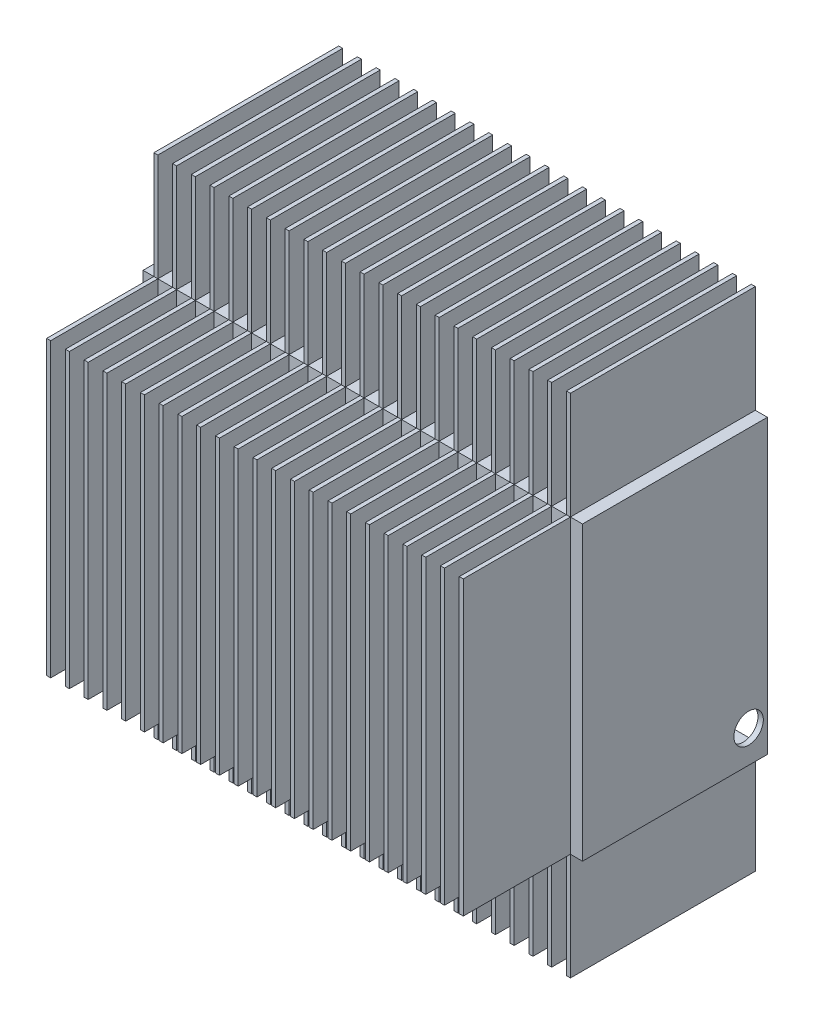
SolidWorks part; units mm, degrees
ref_plane "Front Plane" through (0, 0, 0) normal (0, 0, 1) x (1, 0, 0)
ref_plane "Top Plane" through (0, 0, 0) normal (0, 1, 0) x (1, 0, 0)
ref_plane "Right Plane" through (0, 0, 0) normal (1, 0, 0) x (0, 0, -1)
sketch "Sketch1" plane through (0, 0, 0) normal (0, 0, 1) x (1, 0, 0)
  line L1 (0, 0) -> (-164, 0)
  line L2 (0, 0) -> (0, 109)
  line L3 (0, 109) -> (-164, 109)
  line L4 (-164, 0) -> (-164, 109)
  dimension "D1" = 164
  dimension "D2" = 109
extrude "Boss-Extrude1" add sketch "Sketch1" against normal blind 69
sketch "Sketch2" plane through (0, 0, 0) normal (0, 0, 1) x (1, 0, 0)
  line L0 (0, 109) -> (-164, 109) construction
  line L1 (-160, 109) -> (-158.5, 109)
  line L2 (-160, 109) -> (-160, 0)
  line L3 (-160, 0) -> (-158.5, 0)
  line L4 (-158.5, 109) -> (-158.5, 0)
  line L5 (-164, 0) -> (0, 0) construction
  dimension "D1" = 4
  dimension "D2" = 1.5
extrude "Boss-Extrude3" add sketch "Sketch2" along normal blind 40 contours L2 L3 L4 L1
pattern_linear "LPattern3" count 23 spacing 7 along (1, 0, 0) of "Boss-Extrude3"
ref_plane "Plane1" through (0, 0, -2) normal (0, 0, 1) x (1, 0, 0)
ref_plane "Plane2" through (0, 0, -67) normal (0, 0, 1) x (1, 0, 0)
sketch "Sketch4" plane through (0, 0, -67) normal (0, 0, 1) x (1, 0, 0)
  line L1 (-2, 107) -> (-162, 107)
  line L2 (-2, 107) -> (-2, 2)
  line L3 (-2, 2) -> (-162, 2)
  line L4 (-162, 107) -> (-162, 2)
  dimension "D1" = 2
  dimension "D2" = 2
  dimension "D3" = 2
  dimension "D4" = 2
extrude "Cut-Extrude5" cut sketch "Sketch4" along normal blind 65
ref_plane "Plane3" through (0, 0, 0) normal (0, -1, 0) x (-1, 0, 0)
sketch "Sketch6" plane through (0, 0, 0) normal (0, -1, 0) x (-1, 0, 0)
  line L0 (164, 69) -> (0, 69) construction
  line L1 (4.5, 0) -> (6, 0)
  line L2 (4.5, 0) -> (4.5, 69)
  line L3 (4.5, 69) -> (6, 69)
  line L4 (6, 0) -> (6, 69)
  dimension "D1" = 1.5
extrude "Boss-Extrude4" add sketch "Sketch6" along normal blind 40
pattern_linear "LPattern4" count 23 spacing 7 along (-1, 0, 0) of "Boss-Extrude4"
ref_plane "Plane4" through (0, 109, 0) normal (0, 1, 0) x (1, 0, 0)
sketch "Sketch7" plane through (0, 109, 0) normal (0, 1, 0) x (1, 0, 0)
  line L0 (0, 69) -> (-164, 69) construction
  line L1 (-160, 0) -> (-158.5, 0)
  line L2 (-160, 0) -> (-160, 69)
  line L3 (-160, 69) -> (-158.5, 69)
  line L4 (-158.5, 0) -> (-158.5, 69)
  dimension "D1" = 1.5
extrude "Boss-Extrude5" add sketch "Sketch7" along normal blind 40
pattern_linear "LPattern5" count 23 spacing 7 along (1, 0, 0) of "Boss-Extrude5"
sketch "Sketch15" plane through (0, 0, -67) normal (0, 0, 1) x (1, 0, 0)
  line L1 (-126.06, 109) -> (-164, 109)
  line L2 (-126.06, 109) -> (-126.06, 75)
  line L3 (-126.06, 75) -> (-164, 75)
  line L4 (-164, 109) -> (-164, 75)
  dimension "D1" = 37.94
  dimension "D2" = 34
sketch "Sketch17" plane through (0, 0, -69) normal (0, 0, -1) x (-1, 0, 0)
  line L0 (118, 109) -> (123.5, 109) construction
  line L1 (126.06, 109) -> (113.11, 109)
  line L2 (126.06, 109) -> (126.06, 0)
  line L4 (126.06, 0) -> (113.11, 0)
  line L5 (113.11, 109) -> (113.11, 0)
  line L6 (109.5, 0) -> (104, 0) construction
  dimension "D1" = 12.95
sketch "Sketch19" plane through (0, 0, -2) normal (0, 0, 1) x (1, 0, 0)
  line L1 (-164, 109) -> (-126.06, 109)
  line L2 (-164, 109) -> (-164, 75)
  line L3 (-164, 75) -> (-126.06, 75)
  line L4 (-126.06, 109) -> (-126.06, 75)
  line L5 (-126.06, 109) -> (-113.11, 109)
  line L6 (-126.06, 109) -> (-126.06, 0)
  line L7 (-126.06, 0) -> (-113.11, 0)
  line L8 (-113.11, 109) -> (-113.11, 0)
extrude "Boss-Extrude8" add sketch "Sketch19" against normal blind 55 contours L1 L2 L3 L4
sketch "Sketch20" plane through (0, 0, -2) normal (0, 0, 1) x (1, 0, 0)
  line L1 (-126.06, 109) -> (-113.11, 109)
  line L2 (-126.06, 109) -> (-126.06, 0)
  line L3 (-126.06, 0) -> (-113.11, 0)
  line L4 (-113.11, 109) -> (-113.11, 0)
extrude "Boss-Extrude9" add sketch "Sketch20" against normal blind 51
sketch "Sketch22" plane through (-164, 0, 0) normal (-1, 0, 0) x (0, 0, 1)
  line L0 (-67, -90.2) -> (-67, 90.2) construction
  line L1 (-67, 107) -> (-2, 107)
  line L2 (-67, 107) -> (-67, 2)
  line L3 (-67, 2) -> (-2, 2)
  line L4 (-2, 107) -> (-2, 2)
  line L5 (-2, -90.2) -> (-2, 90.2) construction
  dimension "D1" = 2
  dimension "D2" = 2
sketch "Sketch25" plane through (0, 0, -69) normal (0, 0, -1) x (-1, 0, 0)
  line L1 (39.12, 109) -> (55.25, 109)
  line L2 (39.12, 109) -> (39.12, 0)
  line L3 (39.12, 0) -> (55.25, 0)
  line L4 (55.25, 109) -> (55.25, 0)
  dimension "D2" = 16.13
  dimension "D3" = 39.12
sketch "Sketch26" plane through (0, 0, -2) normal (0, 0, 1) x (1, 0, 0)
  line L1 (-55, 109) -> (-39.12, 109)
  line L2 (-55, 109) -> (-55, 0)
  line L3 (-55, 0) -> (-39.12, 0)
  line L4 (-39.12, 109) -> (-39.12, 0)
extrude "Boss-Extrude10" add sketch "Sketch26" against normal blind 58
sketch "Sketch28" plane through (0, 0, 0) normal (1, 0, 0) x (0, 0, -1)
  line L1 (2, 107) -> (67, 107)
  line L2 (2, 107) -> (2, 2)
  line L3 (2, 2) -> (67, 2)
  line L4 (67, 107) -> (67, 2)
  dimension "D1" = 2
  dimension "D2" = 2
  dimension "D3" = 2
  dimension "D4" = 2
sketch "Sketch29" plane through (-164, 0, 0) normal (-1, 0, 0) x (0, 0, 1)
  circle A0 centre (-58.0023, 9.9396) radius 2
  circle A1 centre (-58.0023, 14.9396) radius 2
  circle A2 centre (-58.0023, 19.9396) radius 2
  circle A3 centre (-58.0023, 27.9396) radius 2
  circle A4 centre (-58.0023, 36.9396) radius 2
  circle A5 centre (-58.0023, 46.9396) radius 2
  circle A6 centre (-58.0023, 56.9396) radius 2
  circle A7 centre (-58.0023, 66.9396) radius 2
  dimension "D1" = 4
  dimension "D2" = 5
  dimension "D6" = 5
  dimension "D3" = 2
  dimension "D4" = 2
  dimension "D5" = 4
extrude "Cut-Extrude12" cut sketch "Sketch29" against normal blind 2
sketch "Sketch31" plane through (0, 0, 0) normal (1, 0, 0) x (0, 0, -1)
  circle A0 centre (62, 12) radius 5.5
  dimension "D1" = 11
  dimension "D2" = 12
  dimension "D3" = 7
extrude "Cut-Extrude13" cut sketch "Sketch31" against normal blind 2
sketch "Sketch32" plane through (0, 0, -69) normal (0, 0, -1) x (-1, 0, 0)
  line L1 (2, 107) -> (162, 107)
  line L2 (2, 107) -> (2, 2)
  line L3 (2, 2) -> (162, 2)
  line L4 (162, 107) -> (162, 2)
  dimension "D1" = 2
  dimension "D2" = 2
  dimension "D3" = 2
  dimension "D4" = 2
extrude "Cut-Extrude14" cut sketch "Sketch32" against normal blind 2
